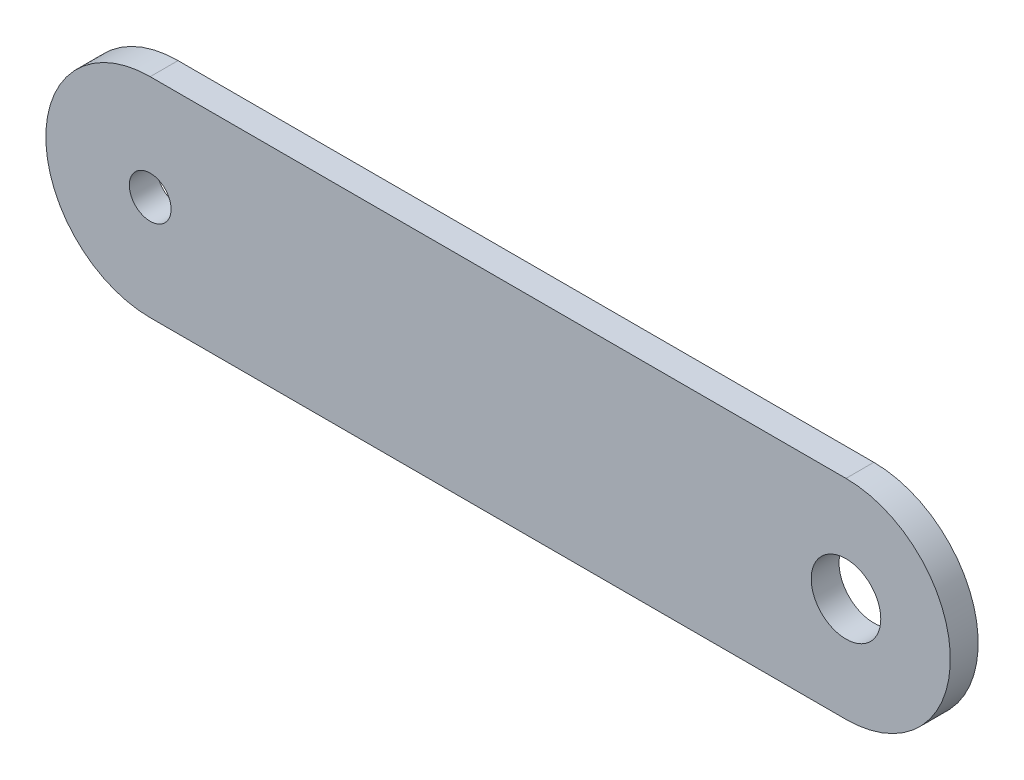
SolidWorks part; units mm, degrees
ref_plane "Front Plane" through (0, 0, 0) normal (0, 0, 1) x (1, 0, 0)
ref_plane "Top Plane" through (0, 0, 0) normal (0, 1, 0) x (1, 0, 0)
ref_plane "Right Plane" through (0, 0, 0) normal (1, 0, 0) x (0, 0, -1)
sketch "Sketch1" plane through (0, 0, 0) normal (0, 0, 1) x (1, 0, 0)
  line L0 (-24.9015, 0) -> (23.202, 0) construction
  line L1 (-25, -7.5) -> (25, -7.5)
  line L3 (-25, 7.5) -> (25, 7.5)
  line L5 (-0.7012, -0.2104) -> (25, 7.5) construction
  line L6 (0.5074, -0.1522) -> (25, -7.5) construction
  line L7 (0, 14.5374) -> (0, -18.0416) construction
  arc A0 (-25, 7.5) -> (-25, -7.5) centre (-25, 0) ccw
  arc A1 (25, -7.5) -> (25, 7.5) centre (25, 0) ccw
  point P1 (0, 0)
  point P9 (-15, -3.75)
  point P10 (25, 0)
  point P11 (-15, -3.75)
  dimension "D1" = 15
  dimension "D2" = 50
  dimension "D3" = 25
extrude "Boss-Extrude1" add sketch "Sketch1" against normal blind 2
sketch "Sketch2" plane through (0, 0, 0) normal (0, 0, 1) x (1, 0, 0)
  line L0 (0, -11.7539) -> (0, 16.5873) construction
  circle A0 centre (-25, 0) radius 1.5
  circle A1 centre (25, 0) radius 2.5
  point P0 (-25, 0)
  point P4 (25, 0)
  dimension "D2" = 5
  dimension "D3" = 3
  dimension "D1" = 25
extrude "Cut-Extrude1" cut sketch "Sketch2" against normal up to next
sketch "Sketch3" plane through (0, 0, 0) normal (0, 0, 1) x (1, 0, 0)
  line L0 (-26.0711, 0) -> (27.6822, 0) construction
equation "\"Length\"= 50"
equation "\"D2@Sketch1\"=\"Length\""
equation "\"Width\"=15"
equation "\"D3@Sketch1\"=\"Length\"/2"
equation "\"D1@Sketch1\"=\"Width\""
equation "\"D1@Sketch2\"=\"Length\"/2"
